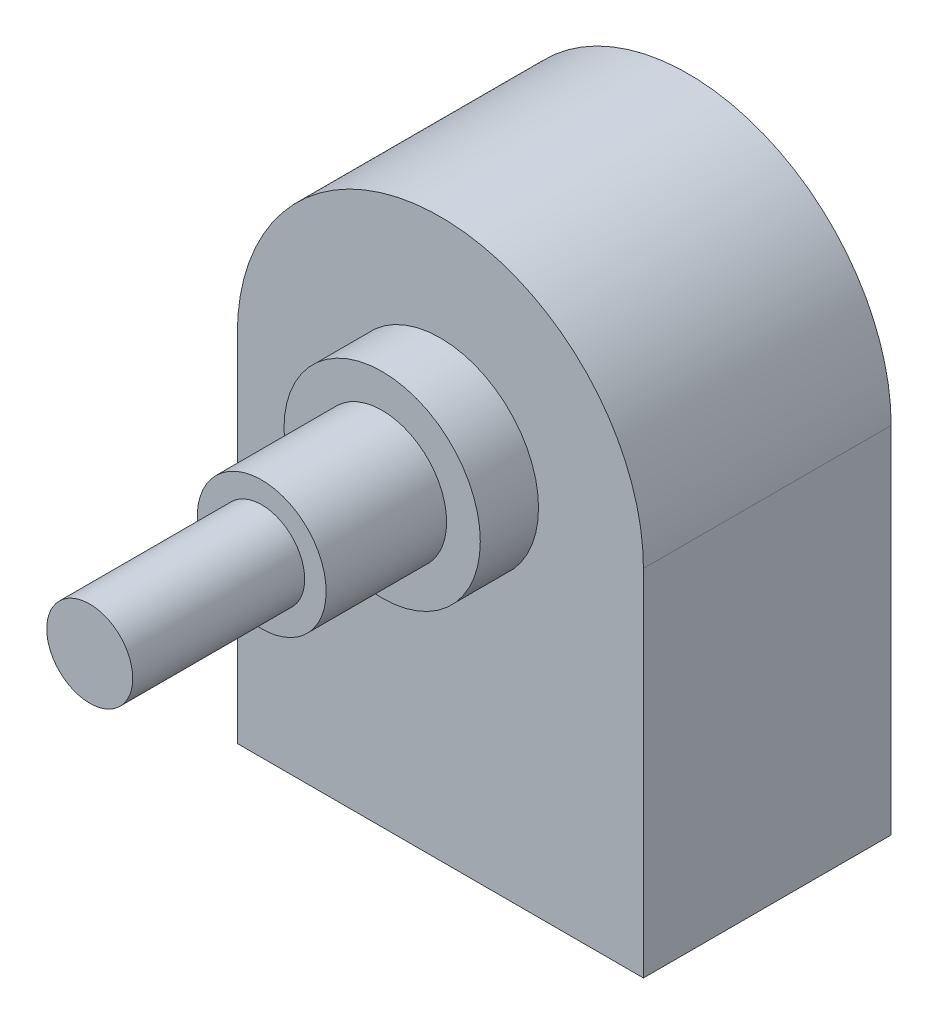
SolidWorks part; units mm, degrees
ref_plane "Plan de face" through (0, 0, 0) normal (0, 0, 1) x (1, 0, 0)
ref_plane "Plan de dessus" through (0, 0, 0) normal (0, 1, 0) x (1, 0, 0)
ref_plane "Plan de droite" through (0, 0, 0) normal (1, 0, 0) x (0, 0, -1)
sketch "Esquisse1" plane through (0, 0, 0) normal (0, 0, 1) x (1, 0, 0)
  line L1 (-15, -13.1) -> (15, -13.1)
  line L2 (-15, -13.1) -> (-15, 13.1)
  line L4 (15, -13.1) -> (15, 13.1)
  line L5 (-15, -13.1) -> (15, 13.1) construction
  line L6 (-15, 13.1) -> (15, -13.1) construction
  arc A0 (-15, 13.1) -> (15, 13.1) centre (0, 13.1) cw
  point P0 (0, 0)
  point P6 (0, 28)
  dimension "D1" = 30
  dimension "D3" = 41.1
extrude "Boss.-Extru.1" add sketch "Esquisse1" along normal blind 18.3
sketch "Esquisse2" plane through (0, 0, 18.3) normal (0, 0, 1) x (1, 0, 0)
  line L0 (-15, 13.1) -> (15, 13.1) construction
  circle A0 centre (0, 13.1) radius 7.25
extrude "Boss.-Extru.2" add sketch "Esquisse2" along normal blind 4.3
sketch "Esquisse3" plane through (0, 0, 22.6) normal (0, 0, 1) x (1, 0, 0)
  circle A0 centre (0, 13.1) radius 4.7625
extrude "Boss.-Extru.3" add sketch "Esquisse3" along normal blind 8.9
sketch "Esquisse4" plane through (0, 0, 31.5) normal (0, 0, 1) x (1, 0, 0)
  circle A0 centre (0, 13.1) radius 3.175
extrude "Boss.-Extru.4" add sketch "Esquisse4" along normal blind 12.7
sketch "Esquisse5" plane through (0, -13.1, 0) normal (0, -1, 0) x (1, 0, 0)
  line L0 (-15, 18.3) -> (15, 18.3) construction
  line L2 (7.18, 8.2) -> (-7.18, 8.2)
  line L3 (7.18, 8.2) -> (7.18, 15.3)
  line L4 (7.18, 15.3) -> (-7.18, 15.3)
  line L5 (-7.18, 8.2) -> (-7.18, 15.3)
  line L6 (7.18, 8.2) -> (-7.18, 15.3) construction
  line L7 (7.18, 15.3) -> (-7.18, 8.2) construction
  line L8 (0, 11.75) -> (0, -2.5058) construction
  line L9 (0, 0) -> (0, 6.6245) construction
  point P0 (0, 11.75)
  dimension "D1" = 3
  dimension "D2" = 7.1
  dimension "D3" = 14.36
  dimension "D4" = 0
extrude "Enlèv. mat.-Extru.2" cut sketch "Esquisse5" against normal blind 6
sketch "Esquisse6" plane through (0, -7.1, 0) normal (0, -1, 0) x (1, 0, 0)
  line L0 (-7.18, 15.3) -> (-7.18, 8.2) construction
  line L1 (-5.32, 12.1371) -> (-4.68, 12.1371)
  line L2 (-5.32, 12.1371) -> (-5.32, 12.7771)
  line L3 (-5.32, 12.7771) -> (-4.68, 12.7771)
  line L4 (-4.68, 12.1371) -> (-4.68, 12.7771)
  line L5 (-2.82, 12.7771) -> (-2.18, 12.7771)
  line L6 (-2.18, 12.1371) -> (-2.18, 12.7771)
  line L7 (-2.82, 12.1371) -> (-2.18, 12.1371)
  line L8 (-2.82, 12.1371) -> (-2.82, 12.7771)
  line L9 (-0.32, 12.7771) -> (0.32, 12.7771)
  line L10 (0.32, 12.1371) -> (0.32, 12.7771)
  line L11 (-0.32, 12.1371) -> (0.32, 12.1371)
  line L12 (-0.32, 12.1371) -> (-0.32, 12.7771)
  line L13 (2.18, 12.7771) -> (2.82, 12.7771)
  line L14 (2.82, 12.1371) -> (2.82, 12.7771)
  line L15 (2.18, 12.1371) -> (2.82, 12.1371)
  line L16 (2.18, 12.1371) -> (2.18, 12.7771)
  line L17 (4.68, 12.7771) -> (5.32, 12.7771)
  line L18 (5.32, 12.1371) -> (5.32, 12.7771)
  line L19 (4.68, 12.1371) -> (5.32, 12.1371)
  line L20 (4.68, 12.1371) -> (4.68, 12.7771)
  line L22 (7.18, 8.2) -> (7.18, 15.3) construction
  dimension "D1" = 0.64
  dimension "D2" = 0.64
  dimension "D3" = 1.86
  dimension "D5" = 1.86
  dimension "D4" = 5
extrude "Boss.-Extru.5" add sketch "Esquisse6" along normal blind 8
